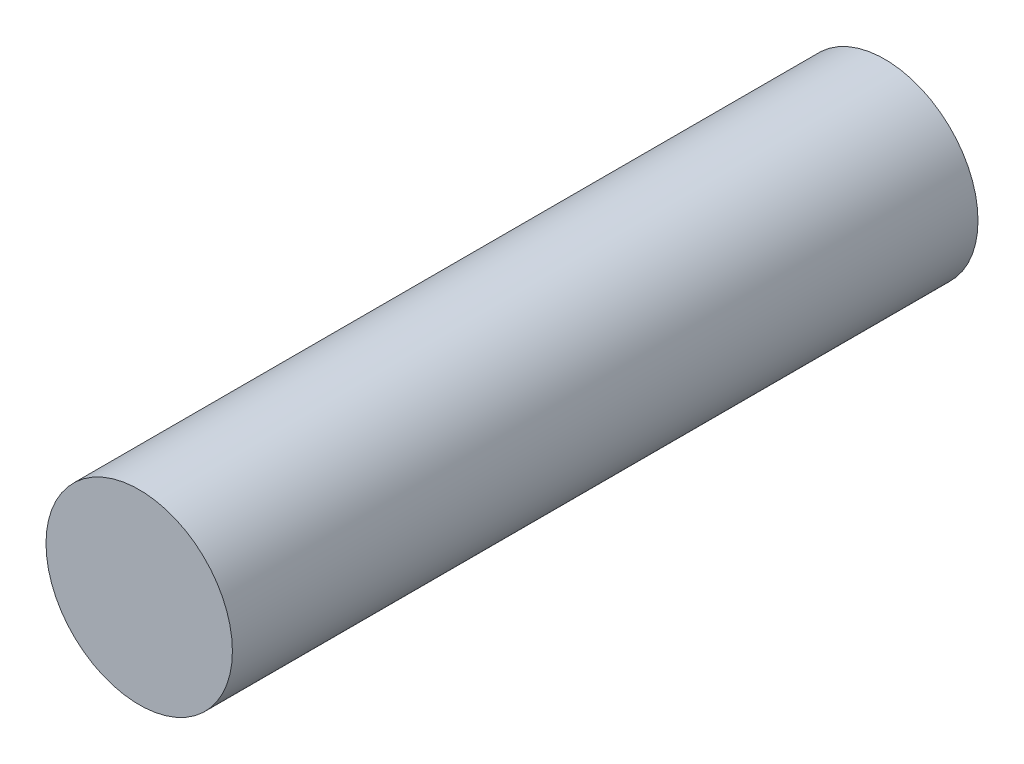
SolidWorks part; units mm, degrees
ref_plane "Front Plane" through (0, 0, 0) normal (0, 0, 1) x (1, 0, 0)
ref_plane "Top Plane" through (0, 0, 0) normal (0, 1, 0) x (1, 0, 0)
ref_plane "Right Plane" through (0, 0, 0) normal (1, 0, 0) x (0, 0, -1)
sketch "Sketch1" plane through (0, 0, 0) normal (0, 0, 1) x (1, 0, 0)
  circle A0 centre (0, 0) radius 5
extrude "Boss-Extrude1" add sketch "Sketch1" along normal blind 40 contours A0
